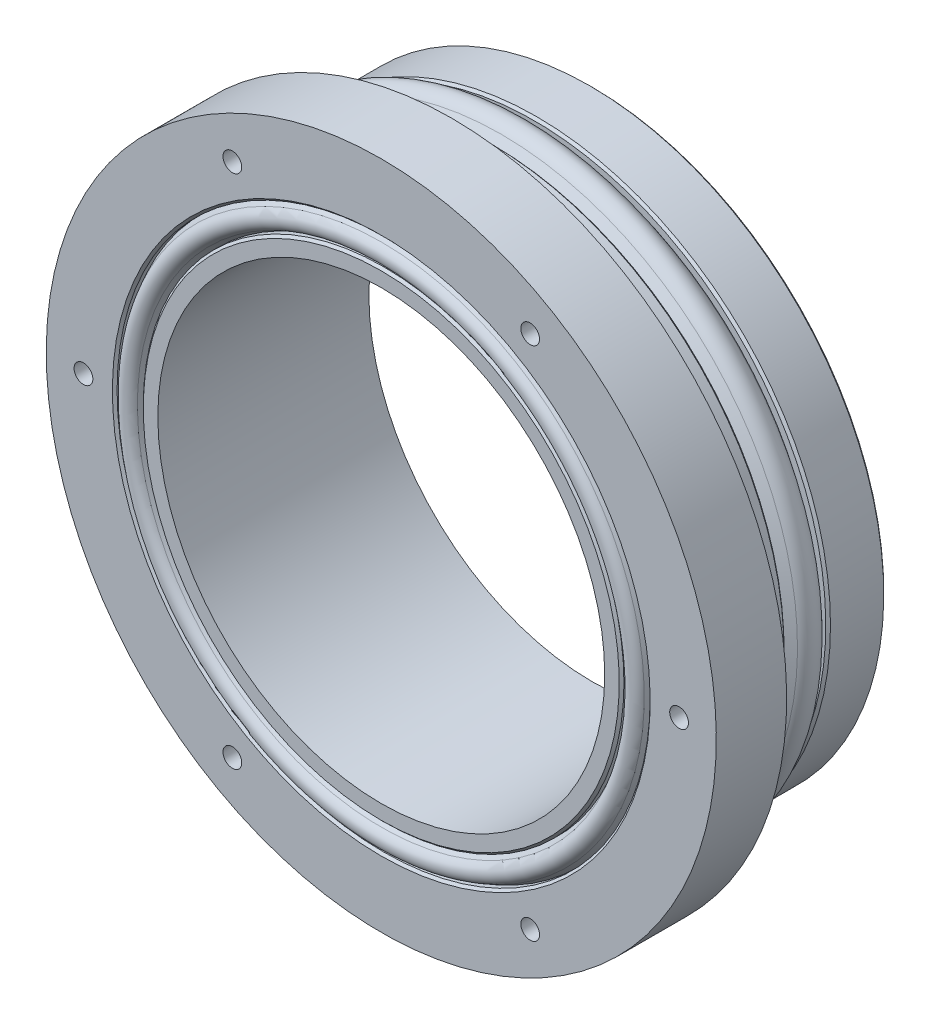
SolidWorks part; units mm, degrees
material "AISI 316 Annealed Stainless Steel Bar (SS)"
ref_plane "Front Plane" through (0, 0, 0) normal (0, 0, 1) x (1, 0, 0)
ref_plane "Top Plane" through (0, 0, 0) normal (0, 1, 0) x (1, 0, 0)
ref_plane "Right Plane" through (0, 0, 0) normal (1, 0, 0) x (0, 0, -1)
sketch "Sketch1" plane through (0, 0, 0) normal (1, 0, 0) x (0, 0, -1)
  line L0 (0, 0) -> (0, 25.4) construction
  line L1 (0, 25.0571) -> (-4.944, 25.0571)
  line L2 (-12, 25.0571) -> (-12, 28.575)
  line L3 (-12, 28.575) -> (-18, 28.575)
  line L4 (-18, 28.575) -> (-18, 22.733)
  line L5 (-18, 19.0571) -> (0, 19.0571)
  line L6 (0, 19.0571) -> (0, 25.0571)
  line L7 (-8.5, 25.0571) -> (-12, 25.0571)
  line L8 (-12, 25.2095) -> (0, 25.2095) construction
  line L9 (0, 0) -> (-18, 0) construction
  line L10 (-18, 0) -> (-18, 19.0571) construction
  line L11 (-8.5, 25.0571) -> (-8.5, 24.2951)
  line L12 (-17.3396, 22.733) -> (-17.9751, 22.4058)
  line L13 (-4.944, 24.2951) -> (-4.944, 25.0571)
  line L14 (-8.5, 24.2951) -> (-7.7635, 25.2643)
  line L15 (-4.944, 24.2951) -> (-5.6805, 25.2643)
  line L16 (-17.3396, 20.4978) -> (-17.9751, 20.825)
  line L17 (0, 25.4) -> (-12, 25.4) construction
  line L18 (-6.722, 25.4) -> (-6.722, 25.781) construction
  line L19 (0, 23.5571) -> (-4, 23.5571) construction
  line L20 (-4, 23.5571) -> (-4, 20.5571) construction
  line L21 (-4, 20.5571) -> (0, 20.5571) construction
  line L22 (-4, 22.0571) -> (0, 22.0571) construction
  line L23 (-18, 20.4978) -> (-17.3396, 20.4978)
  line L24 (-17.3396, 22.733) -> (-17.3396, 20.4978) construction
  line L25 (-17.3396, 22.733) -> (-18, 22.733)
  line L26 (-18, 20.4978) -> (-18, 19.0571)
  line L27 (-18, 26.4) -> (-13, 26.4) construction
  line L28 (-13, 26.4) -> (-13, 24.4) construction
  line L29 (-13, 24.4) -> (-18, 24.4) construction
  line L30 (-13, 25.4) -> (-18, 25.4) construction
  arc A0 (-5.6805, 25.2643) -> (-7.7635, 25.2643) centre (-6.722, 24.4729) ccw
  arc A2 (-17.9751, 22.4058) -> (-17.9751, 20.825) centre (-17.5682, 21.6154) ccw
  point P33 (0, 22.0571)
  dimension "D4" = 2.6162
  dimension "D12" = 3
  dimension "D20" = 1.778
  dimension "D9" = 3.556
  dimension "D1" = 25.4
  dimension "D2" = 3.5
  dimension "D3" = 6
  dimension "D5" = 12
  dimension "D6" = 6
  dimension "D7" = 28.575
  dimension "D8" = 0.762
  dimension "D10" = 19.0571
  dimension "D11" = 50.1142
  dimension "D13" = 4
  dimension "D14" = 0.6604
  dimension "D15" = 2.2352
  dimension "D16" = 20.4978
  dimension "D17" = 2
  dimension "D18" = 25.4
  dimension "D19" = 5
  dimension "D21" = 25.2095
  dimension "D22" = 0.2286
  dimension "D23" = 0.381
revolve "Revolve1" add sketch "Sketch1" angle 360 about L9
sketch "Sketch2" plane through (0, 0, 18) normal (0, 0, 1) x (1, 0, 0)
  circle A0 centre (-25.4, 0) radius 0.8
  circle A1 centre (0, 0) radius 28.575 construction
  circle A2 centre (-12.7, 21.997) radius 0.8
  circle A3 centre (12.7, 21.997) radius 0.8
  circle A4 centre (25.4, 0) radius 0.8
  circle A5 centre (12.7, -21.997) radius 0.8
  circle A6 centre (-12.7, -21.997) radius 0.8
  point P17 (0, 0)
  dimension "D1" = 1.6
  dimension "D2" = 3.175
  dimension "D4" = 50.8
  dimension "D3" = 6
extrude "Cut-Extrude1" cut sketch "Sketch2" against normal blind 3.5
chamfer "Chamfer1" distance 0.2 angle 45 5 edges at (0, 25.0571, 8.5) (0, 25.0571, 0) (0, 22.733, 18) (0, 20.4978, 18) (0, 25.0571, 4.944)
sketch "Sketch3" plane through (0, 0, 0) normal (0, 0, -1) x (-1, 0, 0)
  line L0 (-21.5, 0) -> (0, 0) construction
  line L1 (0, 0) -> (0, 21.5) construction
  line L2 (21.5, 0) -> (0, 0) construction
  line L3 (0, 0) -> (0, -21.5) construction
  circle A0 centre (0, 21.5) radius 1.25
  circle A1 centre (21.5, 0) radius 1.25
  circle A2 centre (0, -21.5) radius 1.25
  circle A3 centre (-21.5, 0) radius 1.25
  circle A4 centre (-21.5, 0) radius 1.5 construction
  dimension "D1" = 2.5
  dimension "D3" = 3
  dimension "D2" = 43
extrude "Cut-Extrude2" cut sketch "Sketch3" against normal blind 4
sketch "Sketch4" plane through (0, 0, 18) normal (0, 0, 1) x (1, 0, 0)
  line L0 (-9.3477, 0) -> (0, 0) construction
  line L1 (0, 0) -> (9.3477, 0) construction
  circle A0 centre (-9.3477, 0) radius 9
  circle A1 centre (9.3477, 0) radius 9
  dimension "D1" = 18
